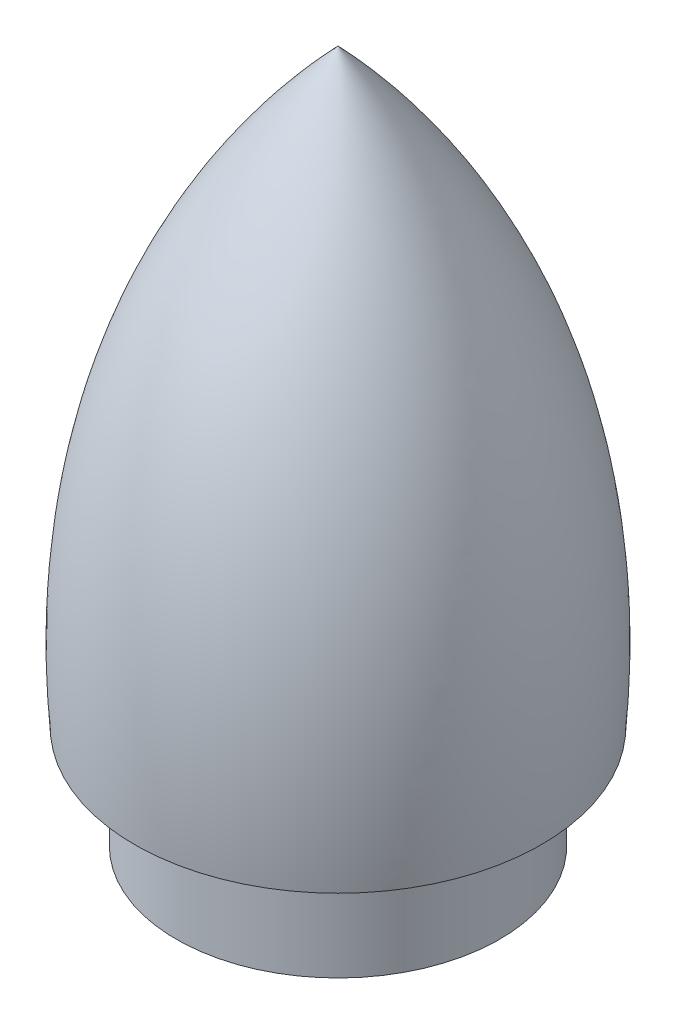
SolidWorks part; units mm, degrees
ref_plane "Front Plane" through (0, 0, 0) normal (0, 0, 1) x (1, 0, 0)
ref_plane "Top Plane" through (0, 0, 0) normal (0, 1, 0) x (1, 0, 0)
ref_plane "Right Plane" through (0, 0, 0) normal (1, 0, 0) x (0, 0, -1)
sketch "Sketch2" plane through (0, 0, 0) normal (0, 0, 1) x (1, 0, 0)
  line L0 (0, 87.0401) -> (0, 0) construction
  line L1 (0, 0) -> (0, -85.7725) construction
  line L2 (-30.2016, 43.0123) -> (0, 43.52) construction
  line L3 (0, 43.52) -> (27.09, 43.52) construction
  line L4 (-15.1008, 43.2662) -> (-12, 43.3183)
  line L5 (-12, 43.3183) -> (-12, 35.6282)
  line L6 (-12, 35.6282) -> (0, 35.6282)
  line L7 (0, 35.6282) -> (0, 87.0401)
  spline S0 degree 2 poles (0, 87.0401) (-17.1565, 69.1521) (-15.1008, 43.2662) knots 0 0 0 1 1 1
  dimension "D1" = 12
revolve "Revolve2" add sketch "Sketch2" angle 360 about L7
sketch "Sketch6" plane through (0, 35.6282, 0) normal (0, -1, 0) x (1, 0, 0)
